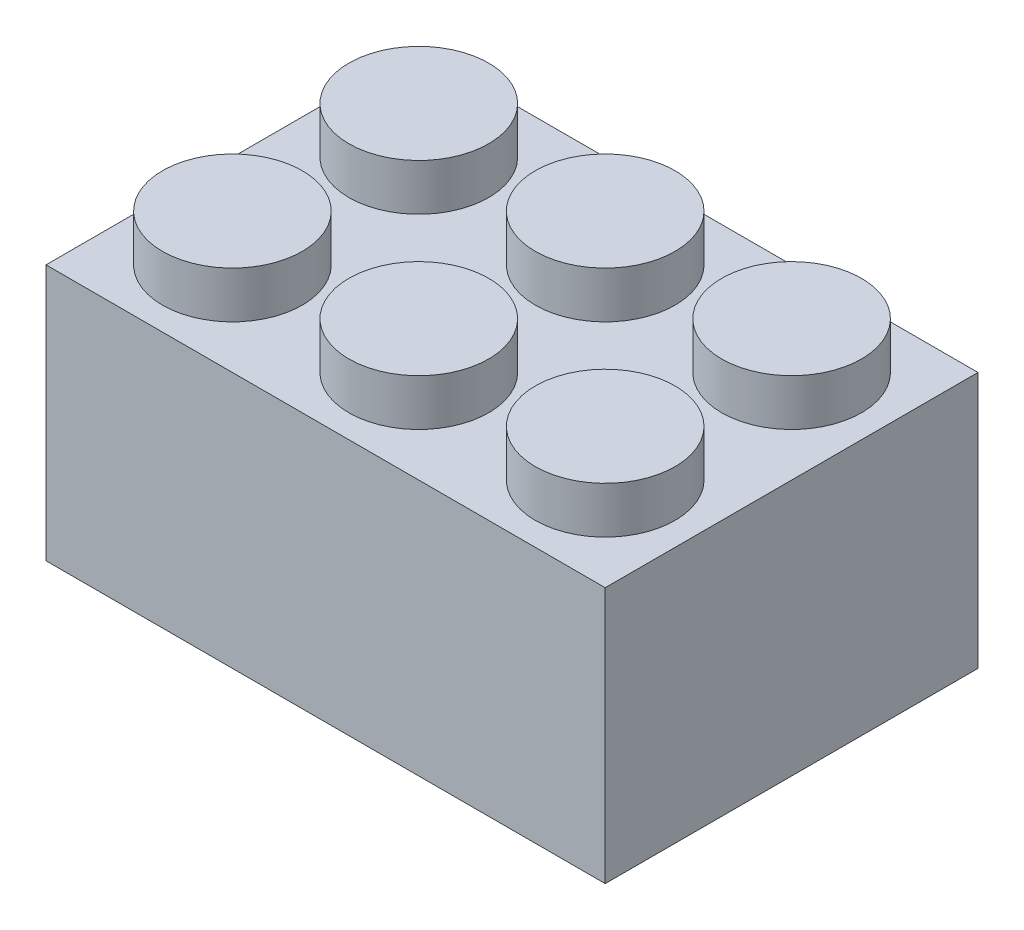
SolidWorks part; units mm, degrees
ref_plane "Front Plane" through (0, 0, 0) normal (0, 0, 1) x (1, 0, 0)
ref_plane "Top Plane" through (0, 0, 0) normal (0, 1, 0) x (1, 0, 0)
ref_plane "Right Plane" through (0, 0, 0) normal (1, 0, 0) x (0, 0, -1)
sketch "Sketch1" plane through (0, 0, 0) normal (0, 1, 0) x (1, 0, 0)
  line L1 (12, -8) -> (-12, -8)
  line L2 (12, -8) -> (12, 8)
  line L3 (12, 8) -> (-12, 8)
  line L4 (-12, -8) -> (-12, 8)
  line L5 (12, -8) -> (-12, 8) construction
  line L6 (12, 8) -> (-12, -8) construction
  point P0 (0, 0)
  dimension "D1" = 24
  dimension "D2" = 16
extrude "Boss-Extrude1" add sketch "Sketch1" along normal blind 11
sketch "Sketch3" plane through (0, 11, 0) normal (0, 1, 0) x (1, 0, 0)
  line L0 (-12, 8) -> (-12, -8) construction
  line L1 (12, 8) -> (-12, 8) construction
  circle A0 centre (-8, 4) radius 3
  dimension "D1" = 6
  dimension "D2" = 4
  dimension "D3" = 4
extrude "Boss-Extrude2" add sketch "Sketch3" along normal blind 2
pattern_linear "LPattern1" count 3 spacing 8 along (1, 0, 0) count 2 spacing 8 along (0, 0, 1) of "Boss-Extrude2"
shell "Shell1" thickness 1
